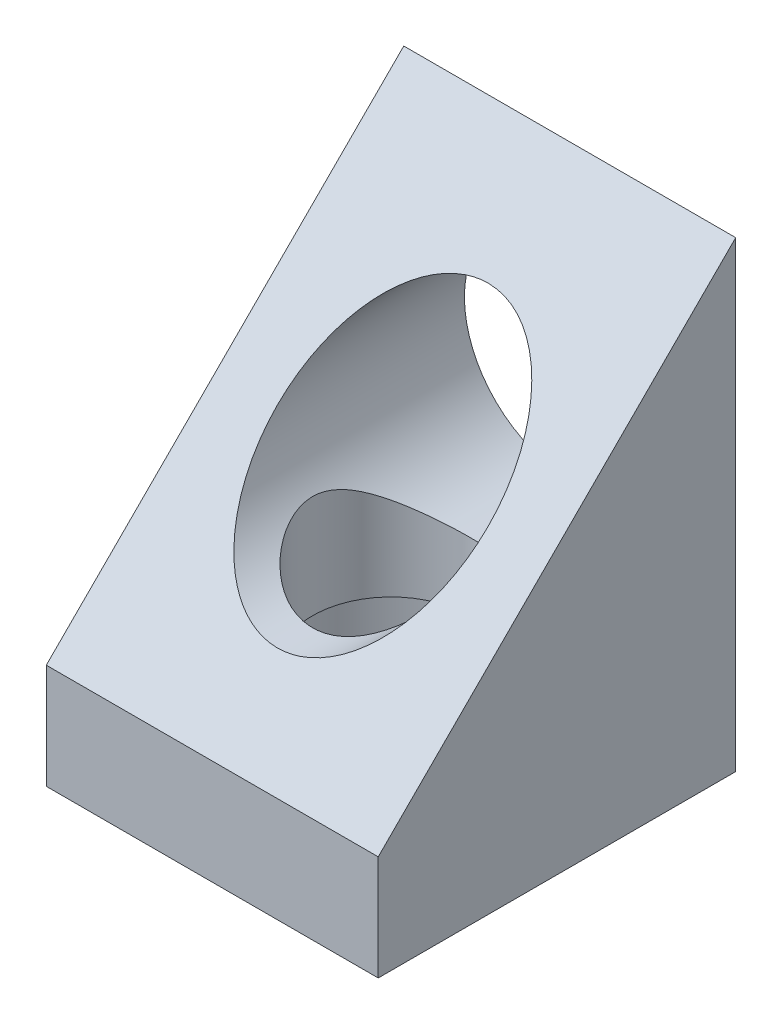
SolidWorks part; units mm, degrees
ref_plane "Front Plane" through (0, 0, 0) normal (0, 0, 1) x (1, 0, 0)
ref_plane "Top Plane" through (0, 0, 0) normal (0, 1, 0) x (1, 0, 0)
ref_plane "Right Plane" through (0, 0, 0) normal (1, 0, 0) x (0, 0, -1)
sketch "Sketch1" plane through (0, 0, 0) normal (1, 0, 0) x (0, 0, -1)
  line L0 (0, 0) -> (28, 0)
  line L1 (28, 0) -> (28, 36.22)
  line L2 (28, 36.22) -> (0, 8.22)
  line L3 (0, 8.22) -> (0, 0)
  dimension "D1" = 28
  dimension "D2" = 8.22
  dimension "D3" = 135
extrude "Boss-Extrude1" add sketch "Sketch1" along normal blind 26
sketch "Sketch2" plane through (0, 0, -28) normal (0, 0, -1) x (-1, 0, 0)
  line L0 (-26, 0) -> (0, 0) construction
  line L1 (-26, 36.22) -> (0, 36.22) construction
  circle A0 centre (-13, 21.58) radius 8.25
  point P7 (-13, 36.22)
  dimension "D1" = 16.5
  dimension "D2" = 21.58
extrude "Cut-Extrude1" cut sketch "Sketch2" against normal through all
sketch "Sketch3" plane through (0, 0, 0) normal (0, -1, 0) x (1, 0, 0)
  line L0 (26, -28) -> (0, -28) construction
  line L1 (26, 0) -> (26, -28) construction
  circle A0 centre (13, -14) radius 6.15
  point P5 (13, -28)
  point P8 (26, -14)
  dimension "D1" = 12.3
extrude "Cut-Extrude2" cut sketch "Sketch3" against normal through all
sketch "Sketch4" plane through (0, 0, 0) normal (0, -1, 0) x (1, 0, 0)
  line L0 (0, 0) -> (0, -28) construction
  line L1 (26, 0) -> (0, 0) construction
  line L2 (26, 0) -> (26, -28) construction
  line L3 (26, -28) -> (0, -28) construction
  circle A0 centre (13, -14) radius 10.325
  circle A1 centre (3.9, -3.85) radius 1.25
  circle A2 centre (23.05, -3.75) radius 1.25
  circle A3 centre (22.85, -22.95) radius 1.25
  circle A4 centre (3.7, -22.65) radius 1.25
  dimension "D1" = 20.65
  dimension "D2" = 2.5
  dimension "D5" = 2.5
  dimension "D8" = 2.5
  dimension "D11" = 2.5
  dimension "D3" = 3.9
  dimension "D4" = 3.85
  dimension "D6" = 2.95
  dimension "D7" = 3.75
  dimension "D9" = 5.05
  dimension "D10" = 3.15
  dimension "D12" = 5.35
  dimension "D13" = 3.7
extrude "Cut-Extrude3" cut sketch "Sketch4" against normal blind 8
